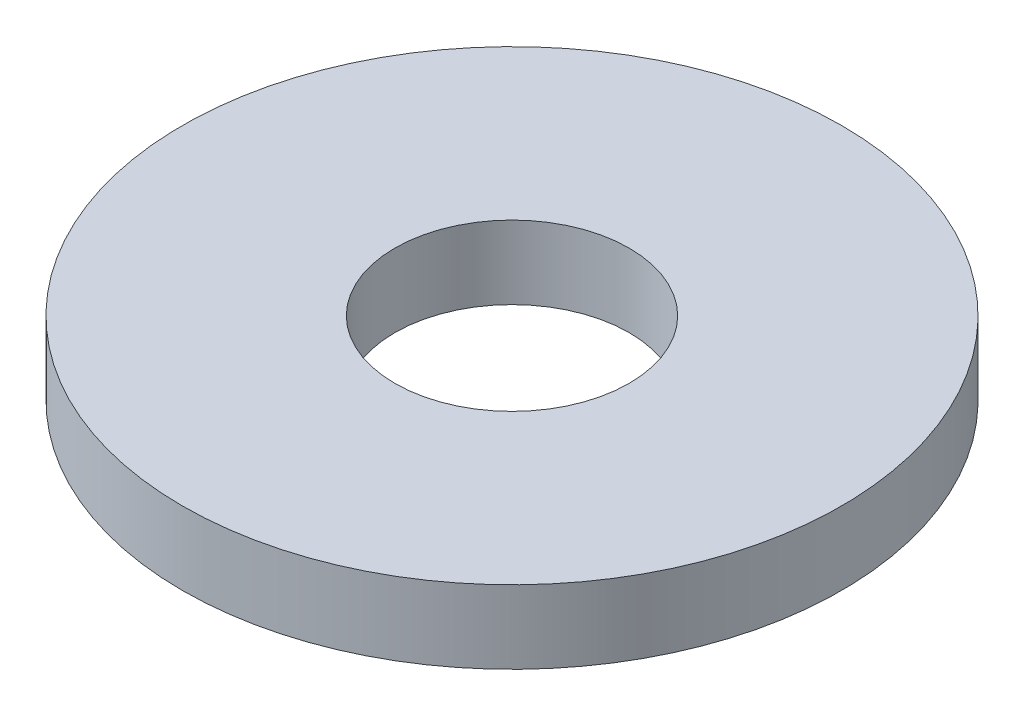
SolidWorks part; units mm, degrees
ref_plane "Front Plane" through (0, 0, 0) normal (0, 0, 1) x (1, 0, 0)
ref_plane "Top Plane" through (0, 0, 0) normal (0, 1, 0) x (1, 0, 0)
ref_plane "Right Plane" through (0, 0, 0) normal (1, 0, 0) x (0, 0, -1)
sketch "Sketch1" plane through (0, 0, 0) normal (0, 1, 0) x (1, 0, 0)
  circle A0 centre (0, 0) radius 1.6
  circle A1 centre (0, 0) radius 4.5
  dimension "D1" = 3.2
  dimension "D2" = 9
extrude "Boss-Extrude1" add sketch "Sketch1" along normal mid plane 1
